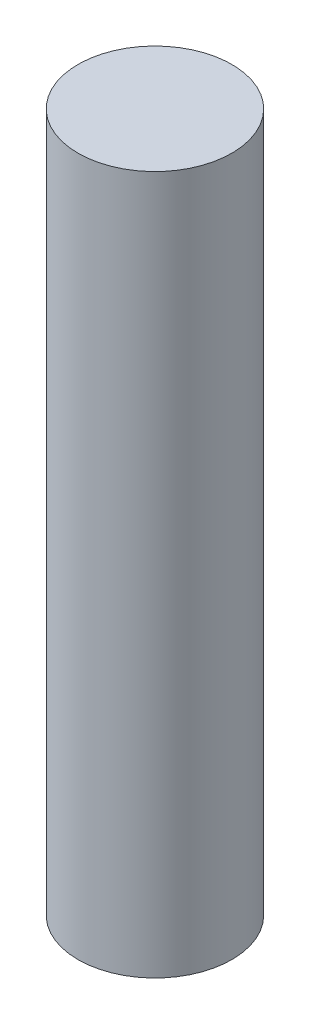
SolidWorks part; units mm, degrees
ref_plane "Front Plane" through (0, 0, 0) normal (0, 0, 1) x (1, 0, 0)
ref_plane "Top Plane" through (0, 0, 0) normal (0, 1, 0) x (1, 0, 0)
ref_plane "Right Plane" through (0, 0, 0) normal (1, 0, 0) x (0, 0, -1)
sketch "Sketch1" plane through (0, 0, 0) normal (0, 1, 0) x (1, 0, 0)
  circle A0 centre (0, 0) radius 6.35
  dimension "D1" = 12.7
extrude "Boss-Extrude1" add sketch "Sketch1" along normal blind 57.658
